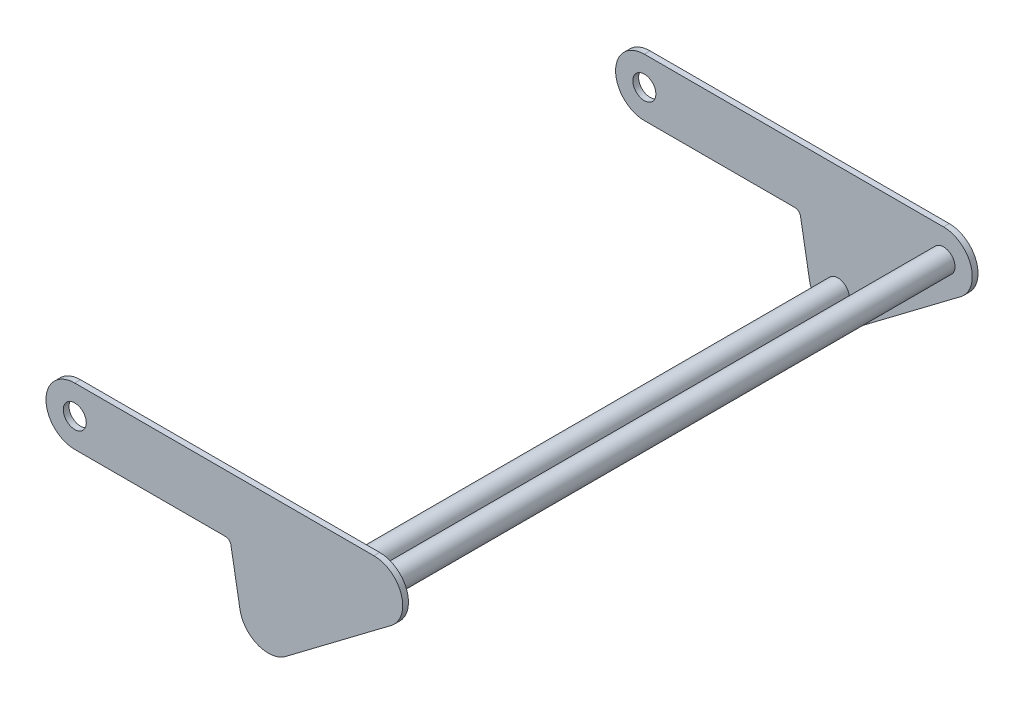
SolidWorks part; units mm, degrees
ref_plane "Front Plane" through (0, 0, 0) normal (0, 0, 1) x (1, 0, 0)
ref_plane "Top Plane" through (0, 0, 0) normal (0, 1, 0) x (1, 0, 0)
ref_plane "Right Plane" through (0, 0, 0) normal (1, 0, 0) x (0, 0, -1)
sketch "Sketch1" plane through (0, 0, 0) normal (0, 0, 1) x (1, 0, 0)
  line L0 (0, 0) -> (166.1217, 0)
  line L1 (182.3313, -61.7111) -> (172.3752, -5.2473)
  line L3 (330.2, 63.5) -> (0, 63.5)
  line L4 (349.3191, 6.402) -> (232.718, -81.5458)
  arc A0 (0, 63.5) -> (0, 0) centre (0, 31.75) ccw
  arc A1 (330.2, 63.5) -> (349.3191, 6.402) centre (330.2, 31.75) cw
  arc A2 (232.718, -81.5458) -> (182.3313, -61.7111) centre (213.599, -56.1977) cw
  circle A3 centre (0, 31.75) radius 12.7
  circle A4 centre (213.599, -56.1977) radius 12.7 construction
  circle A5 centre (330.2, 31.75) radius 12.7 construction
  circle A6 centre (524.3315, -94.1349) radius 76.2 construction
  arc A7 (166.1217, 0) -> (172.3752, -5.2473) centre (166.1217, -6.35) cw
  point P14 (555.0319, 89.7296)
  point P15 (88.2697, 0)
  point P18 (110.7444, -56.9054)
  point P19 (442.3812, -170.2426)
  point P20 (533.8083, 18.2753)
  point P23 (171.45, 0)
  point P24 (447.8847, -143.2278)
  point P25 (567.7078, -125.2349)
  point P26 (535.7894, -126.0533)
  point P27 (524.3315, -94.1349)
  point P28 (165.8171, 0)
  dimension "D1" = 25.4
  dimension "D2" = 31.75
  dimension "D3" = 31.75
  dimension "D4" = 31.75
  dimension "D8" = 152.4
  dimension "D7" = 6.35
  dimension "D5" = 158.75
  dimension "D6" = 146.05
  dimension "D9" = 330.2
  dimension "D10" = 100
extrude "Boss-Extrude1" add sketch "Sketch1" along normal mid plane 635
sketch "Sketch2" plane through (0, 63.5, 0) normal (0, 1, 0) x (1, 0, 0)
  line L0 (-31.75, 317.5) -> (-31.75, -317.5) construction
  line L1 (-31.75, -311.15) -> (361.95, -311.15)
  line L2 (-31.75, -311.15) -> (-31.75, 311.15)
  line L3 (-31.75, 311.15) -> (361.95, 311.15)
  line L4 (361.95, -311.15) -> (361.95, 311.15)
  line L5 (361.95, -317.5) -> (361.95, 317.5) construction
  line L6 (330.2, 317.5) -> (0, 317.5) construction
  line L7 (330.2, -317.5) -> (0, -317.5) construction
  dimension "D1" = 6.35
  dimension "D2" = 6.35
extrude "Cut-Extrude1" cut sketch "Sketch2" against normal through all
sketch "Sketch3" plane through (0, 0, 0) normal (0, 0, 1) x (1, 0, 0)
  circle A0 centre (330.2, 31.75) radius 12.7 construction
  circle A1 centre (213.599, -56.1977) radius 12.7 construction
  circle A3 centre (330.2, 31.75) radius 12.7
  circle A4 centre (213.599, -56.1977) radius 12.7
extrude "Boss-Extrude2" add sketch "Sketch3" along normal up to next and the other way up to next
